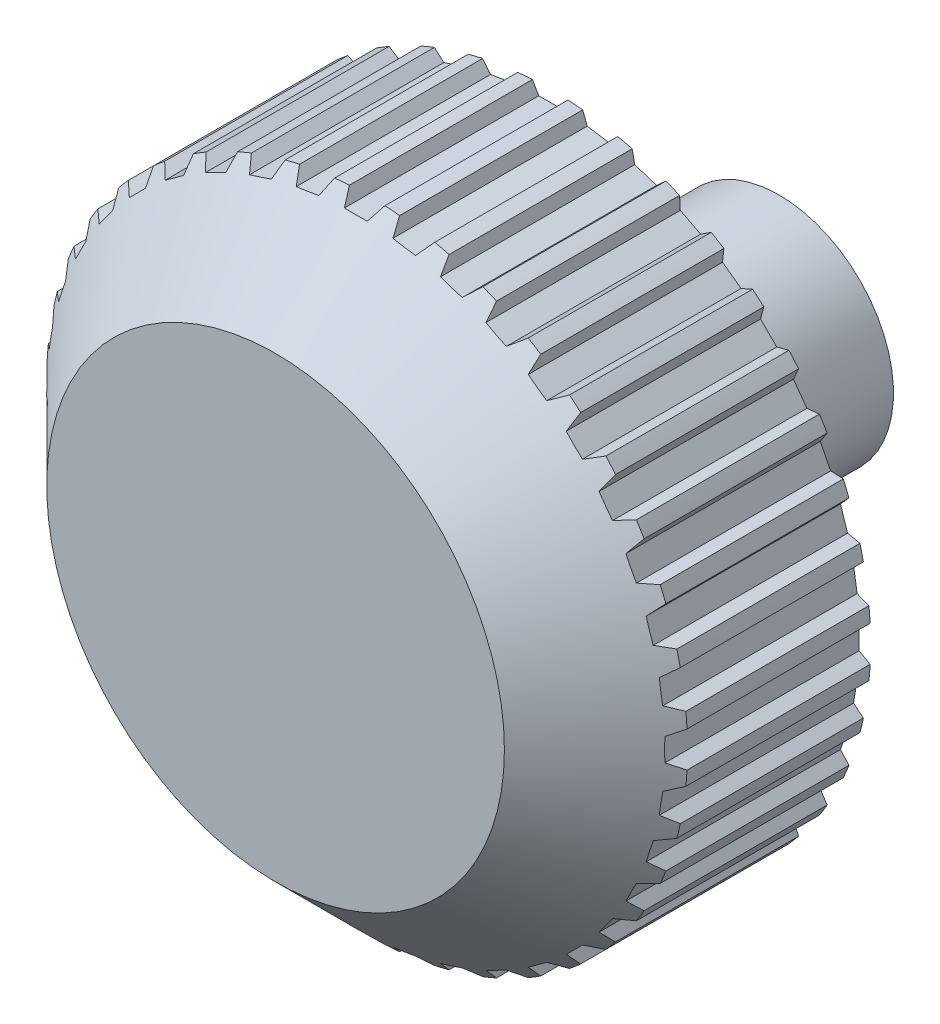
SolidWorks part; units mm, degrees
ref_plane "Plan de face" through (0, 0, 0) normal (0, 0, 1) x (1, 0, 0)
ref_plane "Plan de dessus" through (0, 0, 0) normal (0, 1, 0) x (1, 0, 0)
ref_plane "Plan de droite" through (0, 0, 0) normal (1, 0, 0) x (0, 0, -1)
sketch "Esquisse1" plane through (0, 0, 0) normal (0, 0, 1) x (1, 0, 0)
  circle A0 centre (0, 0) radius 14
  dimension "D1" = 28
extrude "Boss.-Extru.1" add sketch "Esquisse1" along normal blind 12
sketch "Esquisse2" plane through (0, 0, 12) normal (0, 0, 1) x (1, 0, 0)
  line L0 (-1.6547, 15.5) -> (-0.5, 13.5)
  line L1 (-0.5, 13.5) -> (0.5, 13.5)
  line L2 (0.5, 13.5) -> (1.6547, 15.5)
  line L3 (1.6547, 15.5) -> (-1.6547, 15.5)
  line L4 (0, 0) -> (0, 21.1749) construction
  circle A0 centre (0, 0) radius 14 construction
  dimension "D1" = 60
  dimension "D2" = 120
  dimension "D3" = 1
  dimension "D4" = 0.5
  dimension "D5" = 13.5
  dimension "D6" = 2
extrude "Enlèv. mat.-Extru.1" cut sketch "Esquisse2" against normal through all
sketch "Esquisse3" plane through (0, 0, 0) normal (1, 0, 0) x (0, 0, -1)
  line L0 (-18.0975, 0) -> (6.4366, 0) construction
sketch "Esquisse4" plane through (0, 0, 0) normal (0, 0, 1) x (1, 0, 0)
  line L0 (-17.1579, 0) -> (18.8007, 0) construction
pattern_circular "Répétition circulaire1" count 40 over 360 about axis through (0, 0, 0) along (0, 0, 1) of "Enlèv. mat.-Extru.1"
sketch "Esquisse5" plane through (0, 0, 0) normal (0, 1, 0) x (1, 0, 0)
  line L0 (10, -12) -> (14, -8)
  line L1 (14, -8) -> (14, -12)
  line L2 (14, -12) -> (10, -12)
  line L3 (0, -18.0975) -> (0, 6.4366) construction
  line L4 (-17.1579, 0) -> (18.8007, 0) construction
  dimension "D1" = 14
  dimension "D2" = 12
  dimension "D3" = 4
  dimension "D4" = 4
revolve "Enlèvement de matière-Révolution1" cut sketch "Esquisse5" angle 360 about L0
sketch "Esquisse6" plane through (0, 0, 0) normal (0, 0, -1) x (-1, 0, 0)
  circle A0 centre (0, 0) radius 12
  dimension "D1" = 24
extrude "Enlèv. mat.-Extru.2" cut sketch "Esquisse6" against normal blind 6
sketch "Esquisse7" plane through (0, 0, 6) normal (0, 0, -1) x (-1, 0, 0)
  circle A0 centre (0, 0) radius 5
  dimension "D1" = 10
extrude "Boss.-Extru.2" add sketch "Esquisse7" along normal blind 16
sketch "Esquisse8" plane through (0, 0, -10) normal (0, 0, -1) x (-1, 0, 0)
  circle A0 centre (0, 0) radius 3.1
  dimension "D1" = 6.2
extrude "Enlèv. mat.-Extru.3" cut sketch "Esquisse8" against normal blind 10
sketch "Esquisse9" plane through (0, 0, 0) normal (0, 0, -1) x (-1, 0, 0)
  line L0 (-1.5, -2.7129) -> (-1.5, 2.7129)
  circle A0 centre (0, 0) radius 3.1 construction
  arc A1 (-1.5, -2.7129) -> (-1.5, 2.7129) centre (0, 0) cw
  dimension "D1" = 1.5
extrude "Boss.-Extru.3" add sketch "Esquisse9" along normal blind 6
